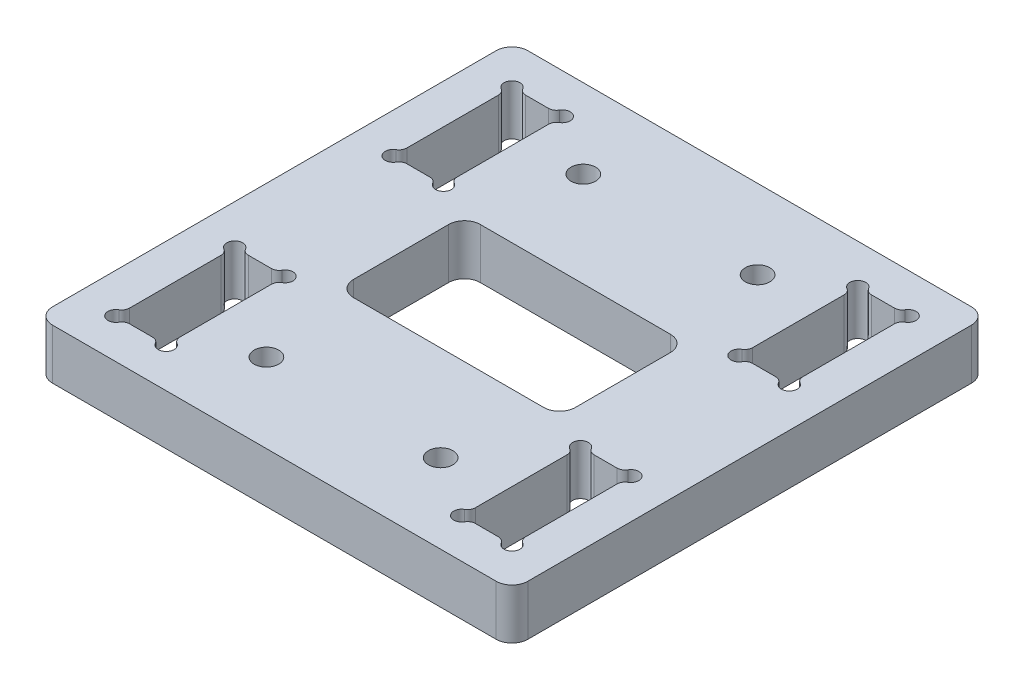
SolidWorks part; units mm, degrees
ref_plane "Front Plane" through (0, 0, 0) normal (0, 0, 1) x (1, 0, 0)
ref_plane "Top Plane" through (0, 0, 0) normal (0, 1, 0) x (1, 0, 0)
ref_plane "Right Plane" through (0, 0, 0) normal (1, 0, 0) x (0, 0, -1)
sketch "Sketch1" plane through (0, 0, 0) normal (0, 1, 0) x (1, 0, 0)
  line L0 (-30, 30) -> (30, 30)
  line L1 (-30, 30) -> (-30, -30)
  line L2 (30, 30) -> (30, -30)
  line L3 (-30, -30) -> (30, -30)
  line L4 (30, -30) -> (-30, 30) construction
  point P0 (0, 0)
  point P3 (30, -26.0769)
  dimension "D1" = 60
  dimension "D2" = 60
extrude "Boss-Extrude1" add sketch "Sketch1" along normal blind 6.35
sketch "Sketch2" plane through (0, 6.35, 0) normal (0, 1, 0) x (1, 0, 0)
  line L0 (-14, 8) -> (14, 8)
  line L1 (-14, 8) -> (-14, -8)
  line L2 (14, 8) -> (14, -8)
  line L3 (-14, -8) -> (14, -8)
  line L4 (14, -8) -> (-14, 8) construction
  point P0 (0, 0)
  dimension "D1" = 16
  dimension "D2" = 28
extrude "Cut-Extrude1" cut sketch "Sketch2" against normal through all
hole_wizard "CBORE for M2.5 SHCS1" positions "Sketch3" profile "Sketch4" counterbore size "M2.5" standard "ANSI Metric" end condition up to next
sketch "Sketch3" plane through (0, 0, 0) normal (0, -1, 0) x (-1, 0, 0)
  line L0 (-11, 20) -> (11, 20) construction
  line L1 (-11, 20) -> (-11, -20) construction
  line L2 (11, 20) -> (11, -20) construction
  line L3 (-11, -20) -> (11, -20) construction
  line L4 (11, -20) -> (-11, 20) construction
  point P0 (-11, 20)
  point P2 (11, 20)
  point P4 (-11, -20)
  point P6 (11, -20)
  point P40 (0, 0)
  point P41 (-22.7699, 16.6275)
  point P42 (0, 0)
  point P44 (0, 0)
  point P45 (11, 20)
  point P46 (-11, 20)
  point P47 (-11, -20)
  point P48 (11, -20)
  dimension "D1" = 40
  dimension "D2" = 22
sketch "Sketch4" plane through (11, 0, -20) normal (1, 0, 0) x (0, 0, -1)
  line L0 (0, 0) -> (0, 6.35)
  line L1 (0, 6.35) -> (1.55, 6.35)
  line L3 (1.55, 6.35) -> (1.55, 2.5)
  line L4 (1.55, 2.5) -> (2.75, 2.5)
  line L5 (2.75, 2.5) -> (2.75, 0)
  line L7 (2.75, 0) -> (0, 0)
  line L11 (0, -6.35) -> (0, 107.95) construction
  dimension "Thru Hole Dia." = 3.1
  dimension "Thru Hole Depth" = 6.35
  dimension "C'Bore Dia." = 5.5
  dimension "C'Bore Depth" = 2.5
other "Move Face2" face at (11, 2.5, -21.55) face at (11, 2.5, 18.45) face at (-11, 2.5, 18.45) face at (-11, 2.5, -21.55) parameters "D1"=0.15
sketch "Sketch5" plane through (0, 6.35, 0) normal (0, 1, 0) x (1, 0, 0)
  line L0 (18.65, 25) -> (25, 25)
  line L1 (18.65, 25) -> (18.65, 10)
  line L2 (25, 25) -> (25, 10)
  line L3 (18.65, 10) -> (25, 10)
  line L4 (30, -30) -> (30, 30) construction
  line L5 (30, 30) -> (-30, 30) construction
  dimension "D1" = 6.35
  dimension "D2" = 15
  dimension "D3" = 5
  dimension "D4" = 5
extrude "Cut-Extrude2" cut sketch "Sketch5" against normal through all
sketch "Sketch6" plane through (0, 6.35, 0) normal (0, 1, 0) x (1, 0, 0)
  line L0 (25, 25) -> (18.65, 25) construction
  line L1 (18.65, 25) -> (18.65, 10) construction
  line L2 (18.65, 10) -> (25, 10) construction
  line L3 (25, 10) -> (25, 25) construction
  line L4 (23.2679, 25) -> (20.3821, 25)
  line L5 (18.65, 23.2679) -> (18.65, 11.7321)
  line L6 (20.3821, 10) -> (23.2679, 10)
  line L7 (25, 11.7321) -> (25, 23.2679)
  arc A0 (19.516, 25.5) -> (18.15, 24.134) centre (18.65, 25) ccw
  arc A1 (25.5, 24.134) -> (24.134, 25.5) centre (25, 25) ccw
  arc A2 (18.15, 10.866) -> (19.516, 9.5) centre (18.65, 10) ccw
  arc A3 (24.134, 9.5) -> (25.5, 10.866) centre (25, 10) ccw
  arc A4 (18.65, 11.7321) -> (18.15, 10.866) centre (17.65, 11.7321) cw
  arc A5 (20.3821, 25) -> (19.516, 25.5) centre (20.3821, 26) cw
  arc A6 (18.15, 24.134) -> (18.65, 23.2679) centre (17.65, 23.2679) cw
  arc A7 (25, 23.2679) -> (25.5, 24.134) centre (26, 23.2679) cw
  arc A8 (24.134, 25.5) -> (23.2679, 25) centre (23.2679, 26) cw
  arc A9 (23.2679, 10) -> (24.134, 9.5) centre (23.2679, 9) cw
  arc A10 (25.5, 10.866) -> (25, 11.7321) centre (26, 11.7321) cw
  arc A11 (19.516, 9.5) -> (20.3821, 10) centre (20.3821, 9) cw
  dimension "D1" = 2
  dimension "1" = 1
  dimension "D4" = 1
  dimension "D5" = 1
  dimension "D6" = 1
extrude "Cut-Extrude3" cut sketch "Sketch6" against normal through all
mirror "Mirror1" about plane through (0, 0, 0) normal (0, 0, 1) of "Cut-Extrude3"
mirror "Mirror2" about plane through (0, 0, 0) normal (1, 0, 0) of "Mirror1", "Cut-Extrude3"
fillet "Fillet1" radius 2 8 edges at (14, 3.175, 8) (14, 3.175, -8) (-14, 3.175, -8) (-14, 3.175, 8) (30, 3.175, -30) (30, 3.175, 30) (-30, 3.175, 30) (-30, 3.175, -30)
